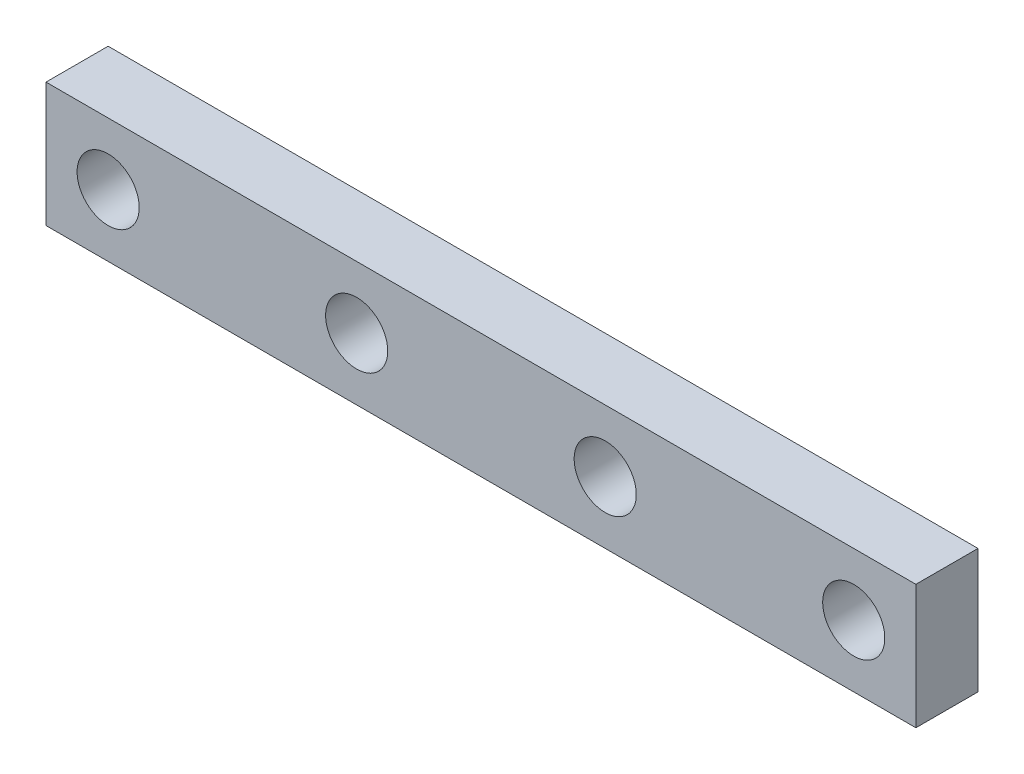
SolidWorks part; units mm, degrees
ref_plane "Front Plane" through (0, 0, 0) normal (0, 0, 1) x (1, 0, 0)
ref_plane "Top Plane" through (0, 0, 0) normal (0, 1, 0) x (1, 0, 0)
ref_plane "Right Plane" through (0, 0, 0) normal (1, 0, 0) x (0, 0, -1)
sketch "Sketch2" plane through (0, 0, 0) normal (0, 0, 1) x (1, 0, 0)
  line L1 (-22.225, -3.175) -> (22.225, -3.175)
  line L2 (-22.225, -3.175) -> (-22.225, 3.175)
  line L3 (-22.225, 3.175) -> (22.225, 3.175)
  line L4 (22.225, -3.175) -> (22.225, 3.175)
  line L5 (-22.225, -3.175) -> (22.225, 3.175) construction
  line L6 (-22.225, 3.175) -> (22.225, -3.175) construction
  point P0 (0, 0)
  dimension "D1" = 6.35
  dimension "D2" = 44.45
extrude "Boss-Extrude1" add sketch "Sketch2" along normal blind 3.175
sketch "Sketch3" plane through (0, 0, 3.175) normal (0, 0, 1) x (1, 0, 0)
  line L0 (0, 3.175) -> (0, -3.175) construction
  line L1 (22.225, 3.175) -> (-22.225, 3.175) construction
  line L2 (-22.225, -3.175) -> (22.225, -3.175) construction
  line L3 (-22.225, 0) -> (22.225, 0) construction
  line L4 (-22.225, 3.175) -> (-22.225, -3.175) construction
  line L5 (22.225, -3.175) -> (22.225, 3.175) construction
  circle A0 centre (-6.35, 0) radius 1.5875
  circle A2 centre (-19.05, 0) radius 1.5875
  point P16 (0, 0)
  dimension "D2" = 12.7
  dimension "D3" = 3.175
  dimension "D4" = 3.175
  dimension "D1" = 6.35
extrude "Cut-Extrude1" cut sketch "Sketch3" against normal through all
mirror "Mirror1" about plane through (0, 0, 0) normal (1, 0, 0) of "Cut-Extrude1"
